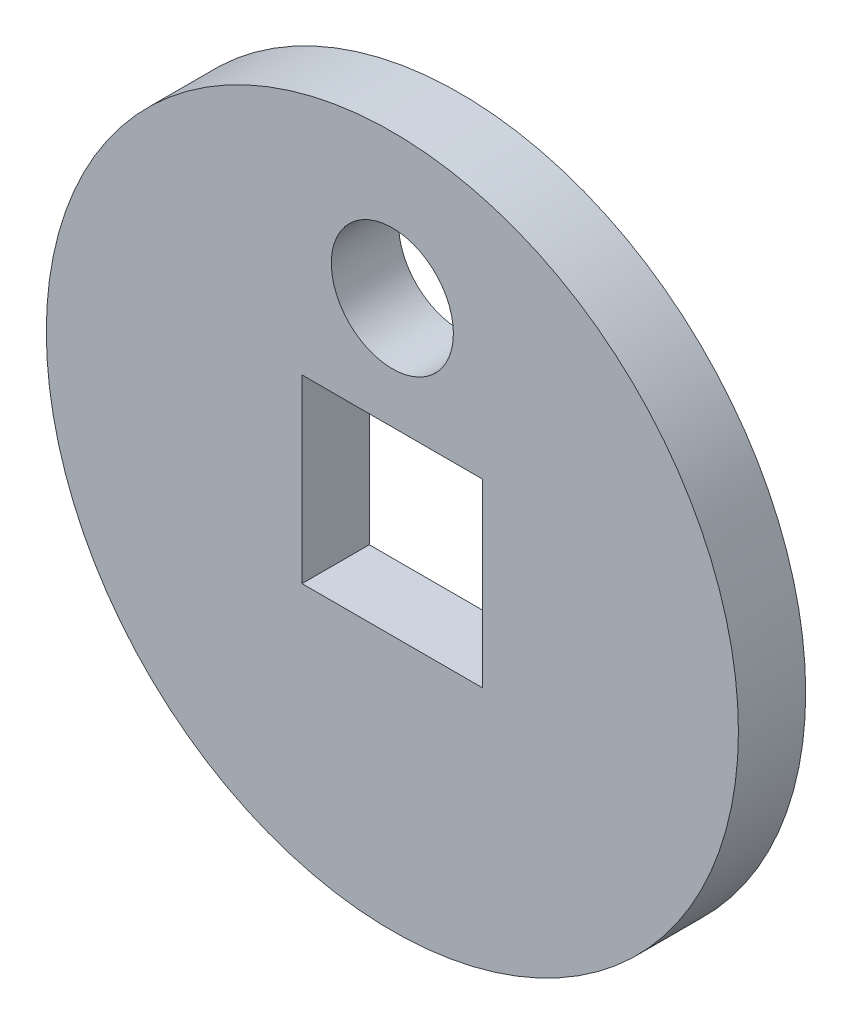
SolidWorks part; units mm, degrees
ref_plane "Front Plane" through (0, 0, 0) normal (0, 0, 1) x (1, 0, 0)
ref_plane "Top Plane" through (0, 0, 0) normal (0, 1, 0) x (1, 0, 0)
ref_plane "Right Plane" through (0, 0, 0) normal (1, 0, 0) x (0, 0, -1)
sketch "Sketch1" plane through (0, 0, 0) normal (0, 0, 1) x (1, 0, 0)
  circle A0 centre (0, 0) radius 9
extrude "Boss-Extrude1" add sketch "Sketch1" along normal blind 1.75
sketch "Sketch2" plane through (0, 0, 1.75) normal (0, 0, 1) x (1, 0, 0)
  line L1 (-2.35, -2.35) -> (2.35, -2.35)
  line L2 (-2.35, -2.35) -> (-2.35, 2.35)
  line L3 (-2.35, 2.35) -> (2.35, 2.35)
  line L4 (2.35, -2.35) -> (2.35, 2.35)
  line L5 (-2.35, -2.35) -> (2.35, 2.35) construction
  line L6 (-2.35, 2.35) -> (2.35, -2.35) construction
  circle A0 centre (0, 5.25) radius 1.5875
  point P0 (0, 0)
  dimension "D1" = 4.7
  dimension "D2" = 4.7
extrude "Cut-Extrude1" cut sketch "Sketch2" against normal through all
